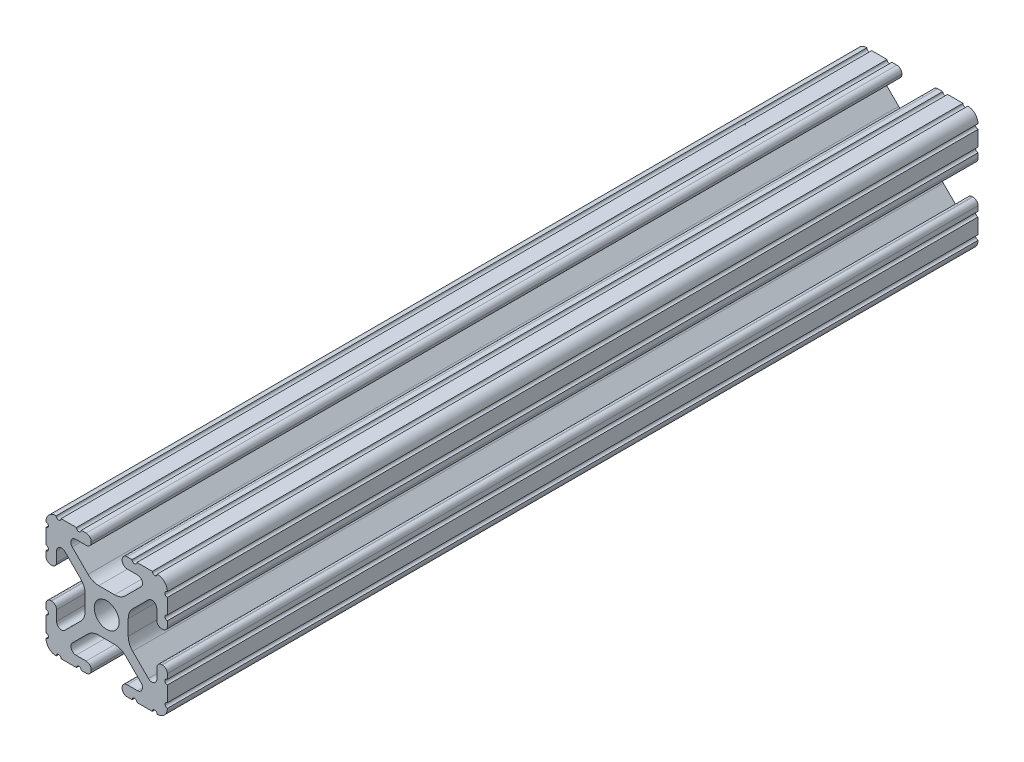
SolidWorks part; units mm, degrees
ref_plane "Front Plane" through (0, 0, 0) normal (0, 0, 1) x (1, 0, 0)
ref_plane "Top Plane" through (0, 0, 0) normal (0, 1, 0) x (1, 0, 0)
ref_plane "Right Plane" through (0, 0, 0) normal (1, 0, 0) x (0, 0, -1)
sketch "Sketch1" plane through (0, 0, 0) normal (0, 0, 1) x (1, 0, 0)
  line L88 (-7.1797, -8.6452) -> (-3.9523, -5.4237)
  line L89 (-1.7093, -4.4958) -> (1.7093, -4.4958)
  line L90 (3.9523, -5.4237) -> (7.1797, -8.6452)
  line L91 (6.4164, -10.4902) -> (4.2875, -10.4902)
  line L92 (3.2385, -11.5392) -> (3.2385, -11.651)
  line L93 (4.2875, -12.7) -> (5.3171, -12.7)
  line L94 (6.3331, -12.7) -> (9.5504, -12.7)
  line L95 (12.7, -9.5504) -> (12.7, -6.3331)
  line L96 (12.7, -5.3171) -> (12.7, -4.2875)
  line L97 (11.651, -3.2385) -> (11.5392, -3.2385)
  line L98 (10.4902, -4.2875) -> (10.4902, -6.4021)
  line L99 (8.7371, -7.1294) -> (5.441, -3.8408)
  line L100 (4.5085, -1.5932) -> (4.5085, 1.5932)
  line L101 (5.441, 3.8408) -> (8.7371, 7.1294)
  line L102 (10.4902, 6.4021) -> (10.4902, 4.2875)
  line L103 (11.5392, 3.2385) -> (11.651, 3.2385)
  line L104 (12.7, 4.2875) -> (12.7, 5.3171)
  line L105 (12.7, 6.3331) -> (12.7, 9.5504)
  line L106 (9.5504, 12.7) -> (6.3331, 12.7)
  line L107 (5.3171, 12.7) -> (4.2875, 12.7)
  line L108 (3.2385, 11.651) -> (3.2385, 11.5392)
  line L109 (4.2875, 10.4902) -> (6.4768, 10.4902)
  line L110 (7.207, 8.7244) -> (3.8983, 5.4232)
  line L111 (1.6558, 4.4958) -> (-1.6558, 4.4958)
  line L112 (-3.8983, 5.4232) -> (-7.207, 8.7244)
  line L113 (-6.4768, 10.4902) -> (-4.2875, 10.4902)
  line L114 (-3.2385, 11.5392) -> (-3.2385, 11.651)
  line L115 (-4.2875, 12.7) -> (-5.3171, 12.7)
  line L116 (-6.3331, 12.7) -> (-9.5504, 12.7)
  line L117 (-12.7, 9.5504) -> (-12.7, 6.3331)
  line L118 (-12.7, 5.3171) -> (-12.7, 4.2875)
  line L119 (-11.651, 3.2385) -> (-11.5392, 3.2385)
  line L120 (-10.4902, 4.2875) -> (-10.4902, 6.4021)
  line L121 (-8.7371, 7.1294) -> (-5.441, 3.8408)
  line L122 (-4.5085, 1.5932) -> (-4.5085, -1.5932)
  line L123 (-5.441, -3.8408) -> (-8.7371, -7.1294)
  line L124 (-10.4902, -6.4021) -> (-10.4902, -4.2875)
  line L125 (-11.5392, -3.2385) -> (-11.651, -3.2385)
  line L126 (-12.7, -4.2875) -> (-12.7, -5.3171)
  line L127 (-12.7, -6.3331) -> (-12.7, -9.5504)
  line L128 (-9.5504, -12.7) -> (-6.3331, -12.7)
  line L129 (-5.3171, -12.7) -> (-4.2875, -12.7)
  line L130 (-3.2385, -11.651) -> (-3.2385, -11.5392)
  line L131 (-4.2875, -10.4902) -> (-6.4164, -10.4902)
  circle A1 centre (0, 0) radius 2.6035
  arc A104 (-7.1797, -8.6452) -> (-6.4164, -10.4902) centre (-6.4164, -9.4098) ccw
  arc A105 (-1.7093, -4.4958) -> (-3.9523, -5.4237) centre (-1.7093, -7.6708) ccw
  arc A106 (3.9523, -5.4237) -> (1.7093, -4.4958) centre (1.7093, -7.6708) ccw
  arc A107 (6.4164, -10.4902) -> (7.1797, -8.6452) centre (6.4164, -9.4098) ccw
  arc A108 (4.2875, -10.4902) -> (3.2385, -11.5392) centre (4.2875, -11.5392) ccw
  arc A109 (3.2385, -11.651) -> (4.2875, -12.7) centre (4.2875, -11.651) ccw
  arc A110 (6.3331, -12.7) -> (5.3171, -12.7) centre (5.8251, -12.7) ccw
  arc A111 (10.5664, -12.6998) -> (9.5504, -12.7) centre (10.0584, -12.7) ccw
  arc A112 (10.5664, -12.6998) -> (12.6998, -10.5664) centre (10.5918, -10.5918) ccw
  arc A113 (12.7, -9.5504) -> (12.6998, -10.5664) centre (12.7, -10.0584) ccw
  arc A114 (12.7, -5.3171) -> (12.7, -6.3331) centre (12.7, -5.8251) ccw
  arc A115 (12.7, -4.2875) -> (11.651, -3.2385) centre (11.651, -4.2875) ccw
  arc A116 (11.5392, -3.2385) -> (10.4902, -4.2875) centre (11.5392, -4.2875) ccw
  arc A117 (8.7371, -7.1294) -> (10.4902, -6.4021) centre (9.4628, -6.4021) ccw
  arc A118 (4.5085, -1.5932) -> (5.441, -3.8408) centre (7.6835, -1.5932) ccw
  arc A119 (5.441, 3.8408) -> (4.5085, 1.5932) centre (7.6835, 1.5932) ccw
  arc A120 (10.4902, 6.4021) -> (8.7371, 7.1294) centre (9.4628, 6.4021) ccw
  arc A121 (10.4902, 4.2875) -> (11.5392, 3.2385) centre (11.5392, 4.2875) ccw
  arc A122 (11.651, 3.2385) -> (12.7, 4.2875) centre (11.651, 4.2875) ccw
  arc A123 (12.7, 6.3331) -> (12.7, 5.3171) centre (12.7, 5.8251) ccw
  arc A124 (12.6998, 10.5664) -> (12.7, 9.5504) centre (12.7, 10.0584) ccw
  arc A125 (12.6998, 10.5664) -> (10.5664, 12.6998) centre (10.5918, 10.5918) ccw
  arc A126 (9.5504, 12.7) -> (10.5664, 12.6998) centre (10.0584, 12.7) ccw
  arc A127 (5.3171, 12.7) -> (6.3331, 12.7) centre (5.8251, 12.7) ccw
  arc A128 (4.2875, 12.7) -> (3.2385, 11.651) centre (4.2875, 11.651) ccw
  arc A129 (3.2385, 11.5392) -> (4.2875, 10.4902) centre (4.2875, 11.5392) ccw
  arc A130 (7.207, 8.7244) -> (6.4768, 10.4902) centre (6.4768, 9.4563) ccw
  arc A131 (1.6558, 4.4958) -> (3.8983, 5.4232) centre (1.6558, 7.6708) ccw
  arc A132 (-3.8983, 5.4232) -> (-1.6558, 4.4958) centre (-1.6558, 7.6708) ccw
  arc A133 (-6.4768, 10.4902) -> (-7.207, 8.7244) centre (-6.4768, 9.4563) ccw
  arc A134 (-4.2875, 10.4902) -> (-3.2385, 11.5392) centre (-4.2875, 11.5392) ccw
  arc A135 (-3.2385, 11.651) -> (-4.2875, 12.7) centre (-4.2875, 11.651) ccw
  arc A136 (-6.3331, 12.7) -> (-5.3171, 12.7) centre (-5.8251, 12.7) ccw
  arc A137 (-10.5664, 12.6998) -> (-9.5504, 12.7) centre (-10.0584, 12.7) ccw
  arc A138 (-10.5664, 12.6998) -> (-12.6998, 10.5664) centre (-10.5918, 10.5918) ccw
  arc A139 (-12.7, 9.5504) -> (-12.6998, 10.5664) centre (-12.7, 10.0584) ccw
  arc A140 (-12.7, 5.3171) -> (-12.7, 6.3331) centre (-12.7, 5.8251) ccw
  arc A141 (-12.7, 4.2875) -> (-11.651, 3.2385) centre (-11.651, 4.2875) ccw
  arc A142 (-11.5392, 3.2385) -> (-10.4902, 4.2875) centre (-11.5392, 4.2875) ccw
  arc A143 (-8.7371, 7.1294) -> (-10.4902, 6.4021) centre (-9.4628, 6.4021) ccw
  arc A144 (-4.5085, 1.5932) -> (-5.441, 3.8408) centre (-7.6835, 1.5932) ccw
  arc A145 (-5.441, -3.8408) -> (-4.5085, -1.5932) centre (-7.6835, -1.5932) ccw
  arc A146 (-10.4902, -6.4021) -> (-8.7371, -7.1294) centre (-9.4628, -6.4021) ccw
  arc A147 (-10.4902, -4.2875) -> (-11.5392, -3.2385) centre (-11.5392, -4.2875) ccw
  arc A148 (-11.651, -3.2385) -> (-12.7, -4.2875) centre (-11.651, -4.2875) ccw
  arc A149 (-12.7, -6.3331) -> (-12.7, -5.3171) centre (-12.7, -5.8251) ccw
  arc A150 (-12.6998, -10.5664) -> (-12.7, -9.5504) centre (-12.7, -10.0584) ccw
  arc A151 (-12.6998, -10.5664) -> (-10.5664, -12.6998) centre (-10.5918, -10.5918) ccw
  arc A152 (-9.5504, -12.7) -> (-10.5664, -12.6998) centre (-10.0584, -12.7) ccw
  arc A153 (-5.3171, -12.7) -> (-6.3331, -12.7) centre (-5.8251, -12.7) ccw
  arc A154 (-4.2875, -12.7) -> (-3.2385, -11.651) centre (-4.2875, -11.651) ccw
  arc A155 (-3.2385, -11.5392) -> (-4.2875, -10.4902) centre (-4.2875, -11.5392) ccw
extrude "Boss-Extrude1" add sketch "Sketch1" along normal mid plane 1828.8
sketch "Sketch2" plane through (12.7, 0, 0) normal (1, 0, 0) x (0, 0, -1)
  line L0 (-842.1091, -105.1) -> (-842.1091, 28.4774) construction
  line L1 (-174.9218, -42.647) -> (-174.9218, 41.3341) construction
  line L2 (-344.6186, 16.7947) -> (-344.6186, -17.9661)
  line L3 (-344.6186, -17.9661) -> (-918.4573, -17.9661)
  line L4 (-918.4573, -17.9661) -> (-918.4573, 16.7947)
  line L5 (-918.4573, 16.7947) -> (-344.6186, 16.7947)
  line L6 (-174.9218, -17.9661) -> (-174.9218, 18.2032)
  line L7 (-174.9218, 18.2032) -> (925.0572, 18.2032)
  line L8 (925.0572, 18.2032) -> (925.0572, -17.9661)
  line L9 (925.0572, -17.9661) -> (-174.9218, -17.9661)
  circle A0 centre (-852.7591, -105.1) radius 10.65 construction
  arc A1 (-164.2718, -31.997) -> (-164.2718, -53.297) centre (-164.2718, -42.647) ccw construction
  point P16 (0, 0)
extrude "Cut-Extrude1" cut sketch "Sketch2" against normal blind 27.432
